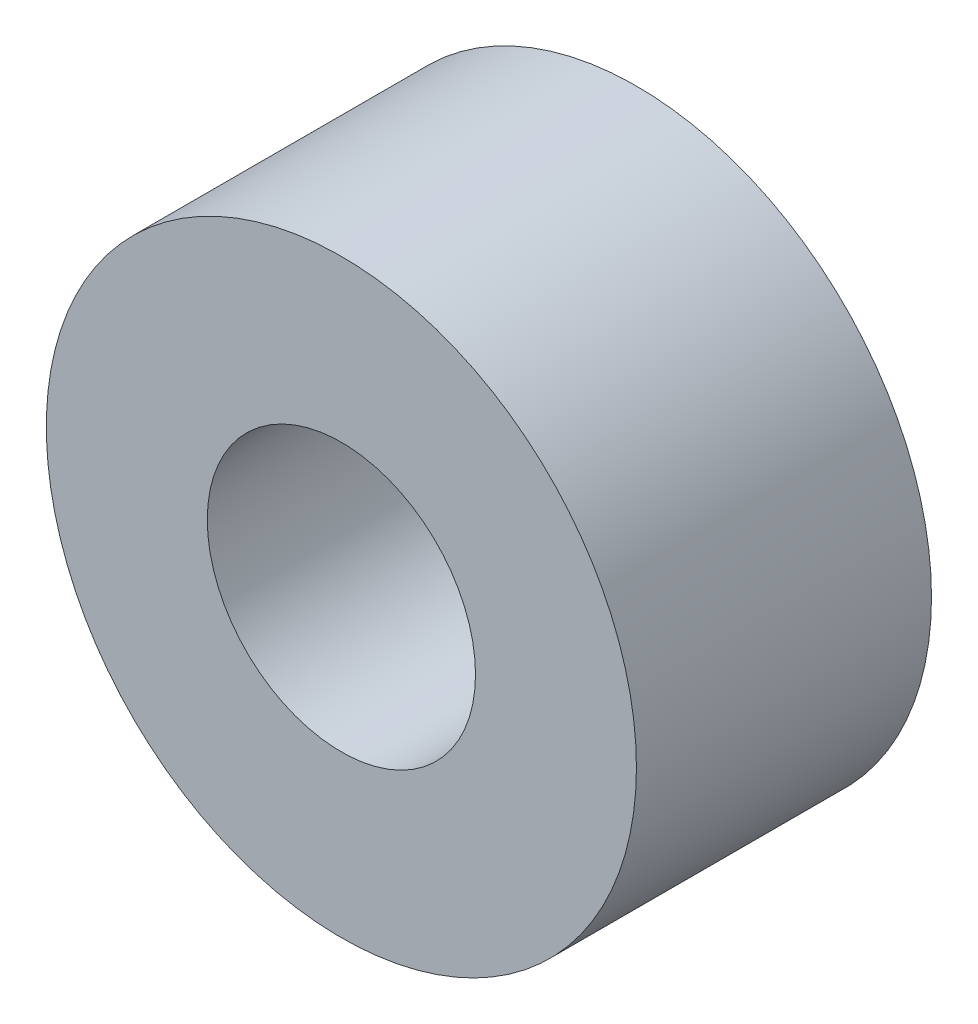
SolidWorks part; units mm, degrees
ref_plane "Front Plane" through (0, 0, 0) normal (0, 0, 1) x (1, 0, 0)
ref_plane "Top Plane" through (0, 0, 0) normal (0, 1, 0) x (1, 0, 0)
ref_plane "Right Plane" through (0, 0, 0) normal (1, 0, 0) x (0, 0, -1)
sketch "Sketch1" plane through (0, 0, 0) normal (0, 0, 1) x (1, 0, 0)
  circle A0 centre (0, 0) radius 2.5
  circle A1 centre (0, 0) radius 5.5
  dimension "D1" = 11
  dimension "D2" = 5
extrude "Boss-Extrude1" add sketch "Sketch1" along normal blind 5.5
